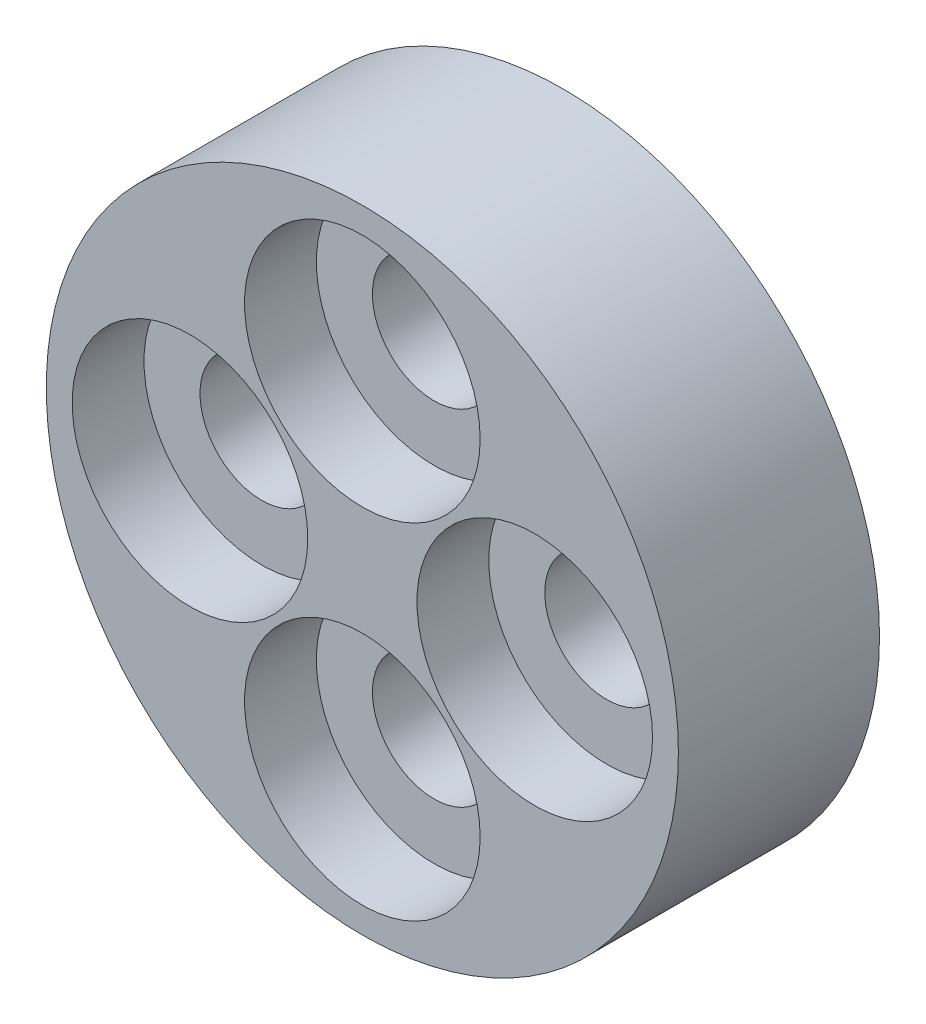
SolidWorks part; units mm, degrees
ref_plane "前视基准面" through (0, 0, 0) normal (0, 0, 1) x (1, 0, 0)
ref_plane "上视基准面" through (0, 0, 0) normal (0, 1, 0) x (1, 0, 0)
ref_plane "右视基准面" through (0, 0, 0) normal (1, 0, 0) x (0, 0, -1)
other "Configuration Table"
sketch "Sketch1" plane through (0, 0, 0) normal (0, 0, 1) x (1, 0, 0)
  circle A0 centre (0, 0) radius 11
  dimension "D1" = 22
extrude "Boss-Extrude1" add sketch "Sketch1" along normal blind 7
sketch "Sketch2" plane through (0, 0, 7) normal (0, 0, 1) x (1, 0, 0)
  circle A0 centre (0, 6) radius 4.1
  circle A1 centre (6, 0) radius 4.1
  circle A2 centre (0, -6) radius 4.1
  circle A3 centre (-6, 0) radius 4.1
  point P3 (1.3729, -0.8086)
  point P4 (0, 0)
  point P13 (0, 0)
  dimension "D1" = 8.2
  dimension "D2" = 6
  dimension "D3" = 4
extrude "Cut-Extrude1" cut sketch "Sketch2" against normal blind 2.5
sketch "Sketch3" plane through (0, 0, 4.5) normal (0, 0, 1) x (1, 0, 0)
  circle A0 centre (0, -6) radius 2.15
  circle A1 centre (-6, 0) radius 2.15
  circle A2 centre (0, 6) radius 2.15
  circle A3 centre (6, 0) radius 2.15
  point P12 (0, 0)
  dimension "D1" = 4.3
  dimension "D2" = 4
extrude "Cut-Extrude2" cut sketch "Sketch3" against normal blind 10
